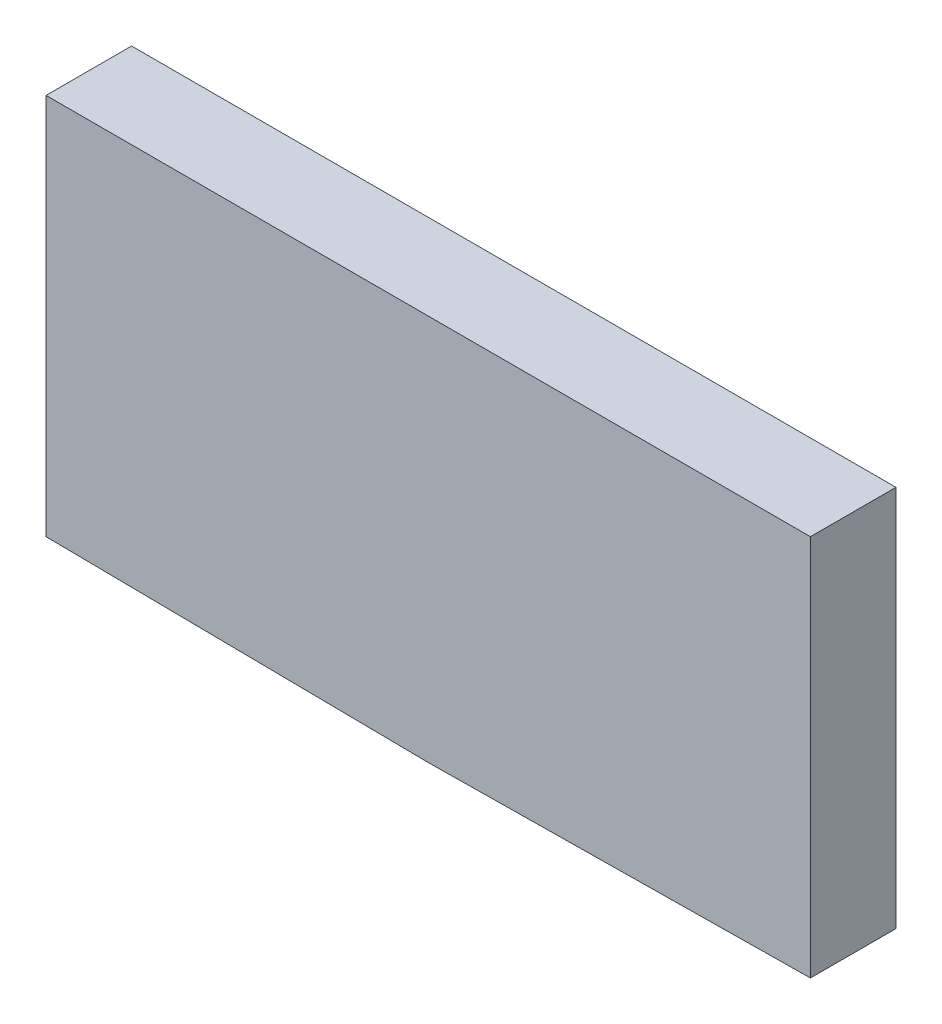
SolidWorks part; units mm, degrees
ref_plane "前视基准面" through (0, 0, 0) normal (0, 0, 1) x (1, 0, 0)
ref_plane "上视基准面" through (0, 0, 0) normal (0, 1, 0) x (1, 0, 0)
ref_plane "右视基准面" through (0, 0, 0) normal (1, 0, 0) x (0, 0, -1)
sketch "草图1" plane through (0, 0, 0) normal (0, 0, 1) x (1, 0, 0)
  line L0 (0, 0) -> (0, 43.0542) construction
  line L1 (0, 0) -> (0, -28.6211) construction
  line L2 (14.3, 14.4682) -> (-14.3, 14.4682)
  line L3 (-14.3, 14.4682) -> (-14.3, 0.1682)
  line L4 (-14.3, 0.1682) -> (0, 0)
  line L5 (14.3, 0.1682) -> (0, 0)
  line L6 (14.3, 14.4682) -> (14.3, 0.1682)
  point P9 (0, 14.4682)
extrude "凸台-拉伸1" add sketch "草图1" along normal blind 3.2
